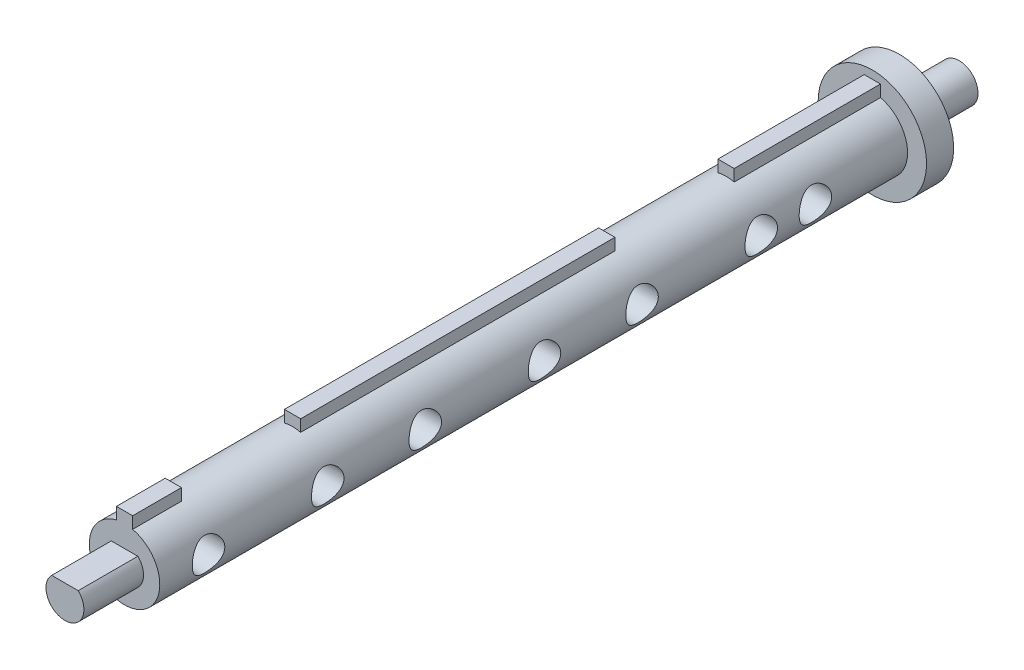
SolidWorks part; units mm, degrees
ref_plane "前视基准面" through (0, 0, 0) normal (0, 0, 1) x (1, 0, 0)
ref_plane "上视基准面" through (0, 0, 0) normal (0, 1, 0) x (1, 0, 0)
ref_plane "右视基准面" through (0, 0, 0) normal (1, 0, 0) x (0, 0, -1)
sketch "草图1" plane through (0, 0, 0) normal (0, 0, 1) x (1, 0, 0)
  line L0 (1.5, 4.5) -> (1.5, 6.3246) construction
  line L1 (-1.5, 4.5) -> (1.5, 4.5) construction
  line L2 (-1.5, 6.3246) -> (-1.5, 8.5)
  line L3 (-1.5, 8.5) -> (1.5, 8.5)
  line L4 (1.5, 6.3246) -> (1.5, 8.5)
  line L5 (0, 6.5) -> (1.5, 8.5) construction
  line L6 (-1.5, 8.5) -> (0, 6.5) construction
  line L7 (0, 6.5) -> (1.5, 4.5) construction
  line L8 (-1.5, 4.5) -> (0, 6.5) construction
  line L9 (-1.5, 4.5) -> (-1.5, 6.3246) construction
  arc A0 (-1.5, 6.3246) -> (1.5, 6.3246) centre (0, 0) ccw
  arc A1 (0, 6.5) -> (-1.5, 6.3246) centre (0, 0) ccw construction
  arc A2 (1.5, 6.3246) -> (0, 6.5) centre (0, 0) ccw construction
  point P3 (0, 6.5)
  dimension "D1" = 13
  dimension "D2" = 2
  dimension "D3" = 3
extrude "凸台-拉伸1" add sketch "草图1" along normal blind 143
sketch "草图2" plane through (0, 0, 143) normal (0, 0, 1) x (1, 0, 0)
  circle A0 centre (0, 0) radius 3.5
  dimension "D1" = 7
extrude "凸台-拉伸2" add sketch "草图2" along normal blind 11
sketch "草图3" plane through (0, 0, 0) normal (0, 0, -1) x (-1, 0, 0)
  circle A0 centre (0, 0) radius 3.5
  dimension "D1" = 7
extrude "凸台-拉伸3" add sketch "草图3" along normal blind 11
sketch "草图4" plane through (0, 0, -11) normal (0, 0, -1) x (-1, 0, 0)
  line L1 (-9.9341, 0) -> (-3.5, 0) construction
  line L2 (-2.4495, -2.5) -> (2.4495, -2.5)
  line L3 (3.5, 0) -> (14.3106, 0) construction
  arc A3 (-2.4495, -2.5) -> (2.4495, -2.5) centre (0, 0) ccw construction
  arc A4 (2.4495, -2.5) -> (-2.4495, -2.5) centre (0, 0) cw
extrude "切除-拉伸1" cut sketch "草图4" against normal blind 11
sketch "草图5" plane through (0, 0, 154) normal (0, 0, 1) x (1, 0, 0)
  line L0 (-2.4495, 2.5) -> (2.4495, 2.5)
  arc A0 (2.4495, 2.5) -> (-2.4495, 2.5) centre (0, 0) ccw
  arc A1 (-2.4495, 2.5) -> (2.4495, 2.5) centre (0, 0) ccw construction
  dimension "D2" = 7
  dimension "D1" = 2.5
extrude "切除-拉伸2" cut sketch "草图5" against normal blind 11
sketch "草图7" plane through (0, 0, 0) normal (1, 0, 0) x (0, 0, -1)
  line L0 (-143, -6.5) -> (0, -6.5) construction
  line L2 (0, -2.5) -> (0, 3.5) construction
  line L3 (0, -6.5) -> (0, 6.3246) construction
  circle A0 centre (-134, 0) radius 3
  circle A1 centre (-112, 0) radius 3
  circle A2 centre (-94, 0) radius 3
  circle A3 centre (-72, 0) radius 3
  circle A4 centre (-54, 0) radius 3
  circle A5 centre (-32, 0) radius 3
  circle A6 centre (-22, 0) radius 3
  dimension "D2" = 6
  dimension "D3" = 6
  dimension "D7" = 6
  dimension "D8" = 6
  dimension "D10" = 6
  dimension "D11" = 6
  dimension "D15" = 6
  dimension "D1" = 22
  dimension "D4" = 6.5
  dimension "D5" = 6.5
  dimension "D6" = 22
  dimension "D9" = 22
  dimension "D12" = 18
  dimension "D13" = 18
  dimension "D14" = 32
  dimension "D16" = 22
extrude "切除-拉伸3" cut sketch "草图7" along normal mid plane 20
sketch "草图9" plane through (0, 0, 0) normal (0, 0, -1) x (-1, 0, 0)
  circle A0 centre (0, 0) radius 10
  dimension "D1" = 20
extrude "凸台-拉伸4" add sketch "草图9" against normal blind 5
sketch "草图10" plane through (1.5, 0, 0) normal (1, 0, 0) x (0, 0, -1)
  line L0 (-143, 8.5) -> (-5, 8.5) construction
  line L2 (-134, 6.3246) -> (-134, 8.5)
  line L3 (-134, 8.5) -> (-112, 8.5)
  line L4 (-112, 6.3246) -> (-112, 8.5)
  line L5 (-134, 6.3246) -> (-112, 6.3246)
  line L6 (-143, 6.3246) -> (-5, 6.3246) construction
  point P0 (-134, 0)
  point P1 (-112, 0)
extrude "切除-拉伸4" cut sketch "草图10" against normal blind 10
sketch "草图12" plane through (0, 0, 112) normal (0, 0, 1) x (1, 0, 0)
  line L0 (-4.5752, 4.6171) -> (4.5752, 4.6171)
  arc A0 (4.5752, 4.6171) -> (-4.5752, 4.6171) centre (0, 0) ccw
extrude "凸台-拉伸5" add sketch "草图12" along normal blind 22
sketch "草图13" plane through (1.5, 0, 0) normal (1, 0, 0) x (0, 0, -1)
  line L0 (-112, 8.5) -> (-5, 8.5) construction
  line L2 (-54, 6.3246) -> (-54, 8.5)
  line L3 (-54, 8.5) -> (-32, 8.5)
  line L4 (-32, 6.3246) -> (-32, 8.5)
  line L5 (-54, 6.3246) -> (-32, 6.3246)
  line L6 (-112, 6.3246) -> (-5, 6.3246) construction
  point P0 (-54, 0)
  point P1 (-32, 0)
extrude "切除-拉伸5" cut sketch "草图13" against normal blind 22
sketch "草图14" plane through (0, 0, 32) normal (0, 0, 1) x (1, 0, 0)
  line L0 (-4.0741, 5.0647) -> (4.0741, 5.0647)
  arc A0 (4.0741, 5.0647) -> (-4.0741, 5.0647) centre (0, 0) ccw
extrude "凸台-拉伸6" add sketch "草图14" along normal blind 22
